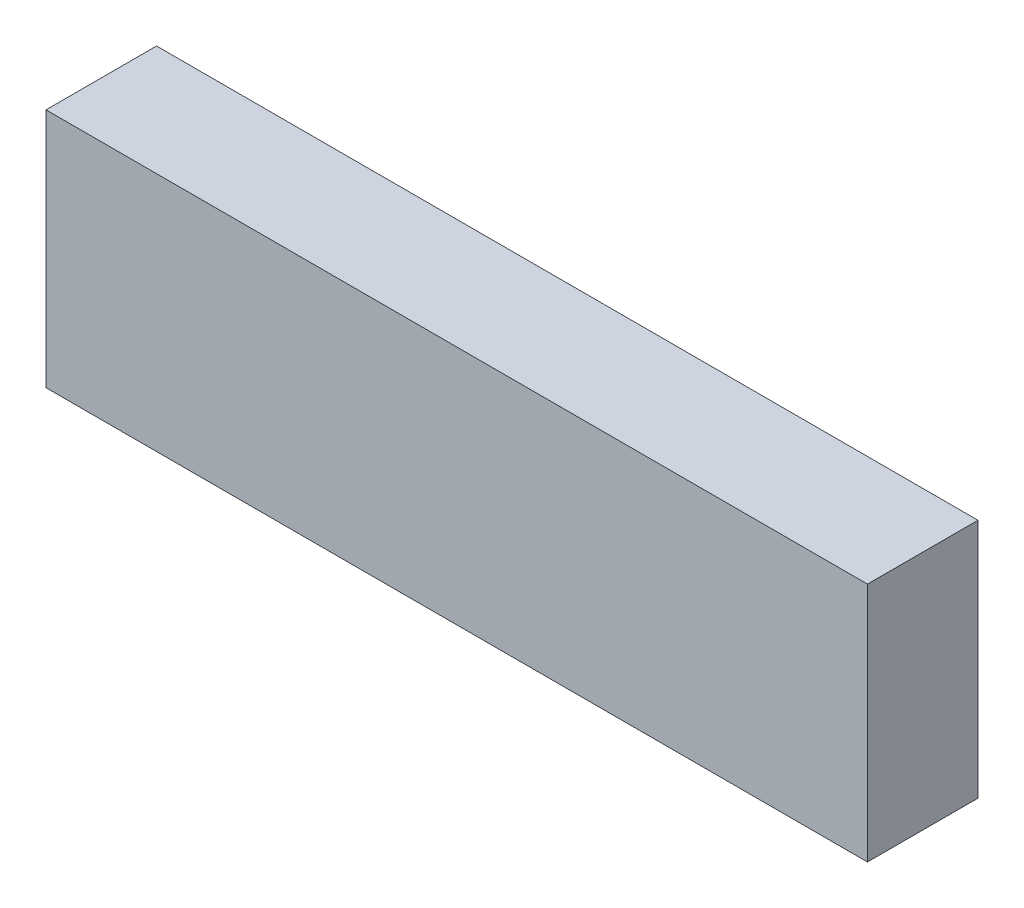
SolidWorks part; units mm, degrees
ref_plane "Front Plane" through (0, 0, 0) normal (0, 0, 1) x (1, 0, 0)
ref_plane "Top Plane" through (0, 0, 0) normal (0, 1, 0) x (1, 0, 0)
ref_plane "Right Plane" through (0, 0, 0) normal (1, 0, 0) x (0, 0, -1)
sketch "Sketch1" plane through (0, 0, 0) normal (0, 0, 1) x (1, 0, 0)
  line L1 (-29.5847, -8.6677) -> (29.5846, -8.6677)
  line L2 (-29.5847, -8.6677) -> (-29.5847, 8.6677)
  line L3 (-29.5847, 8.6677) -> (29.5846, 8.6677)
  line L4 (29.5846, -8.6677) -> (29.5846, 8.6677)
  line L5 (-29.5847, -8.6677) -> (29.5846, 8.6677) construction
  line L6 (-29.5847, 8.6677) -> (29.5846, -8.6677) construction
  point P0 (0, 0)
  dimension "D1" = 59.1693
  dimension "D2" = 17.3355
extrude "Boss-Extrude1" add sketch "Sketch1" along normal blind 7.9629
